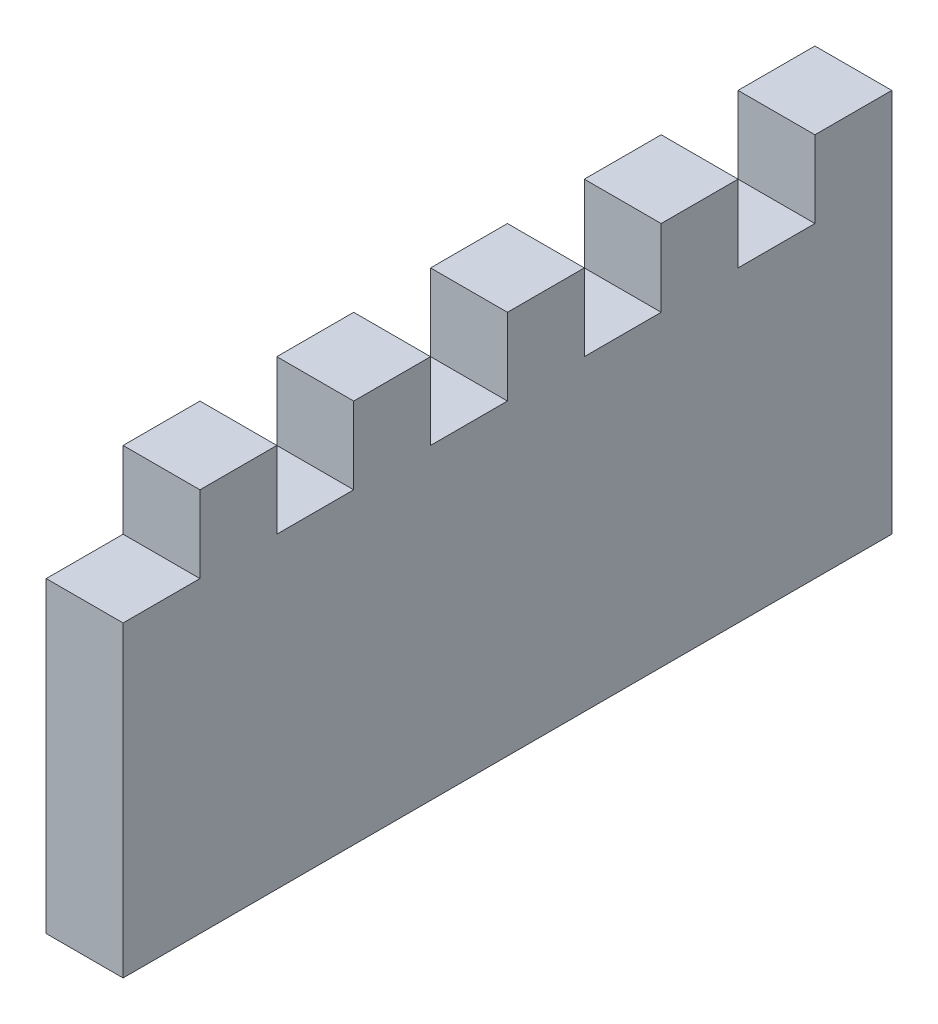
SolidWorks part; units mm, degrees
ref_plane "Plan de face" through (0, 0, 0) normal (0, 0, 1) x (1, 0, 0)
ref_plane "Plan de dessus" through (0, 0, 0) normal (0, 1, 0) x (1, 0, 0)
ref_plane "Plan de droite" through (0, 0, 0) normal (1, 0, 0) x (0, 0, -1)
sketch "Esquisse1" plane through (0, 0, 0) normal (1, 0, 0) x (0, 0, -1)
  line L1 (0, 0) -> (-100, 0)
  line L2 (0, 0) -> (0, 50)
  line L3 (0, 50) -> (-100, 50)
  line L4 (-100, 0) -> (-100, 50)
  dimension "D1" = 100
  dimension "D2" = 50
extrude "Boss.-Extru.1" add sketch "Esquisse1" along normal blind 10
sketch "Esquisse2" plane through (10, 0, 0) normal (1, 0, 0) x (0, 0, -1)
  line L0 (0, 50) -> (-100, 50) construction
  line L1 (-10, 50) -> (-20, 50)
  line L2 (-10, 50) -> (-10, 40)
  line L3 (-10, 40) -> (-20, 40)
  line L4 (-20, 50) -> (-20, 40)
  line L5 (0, 0) -> (0, 50) construction
  dimension "D1" = 10
  dimension "D2" = 10
  dimension "D3" = 10
extrude "Enlèv. mat.-Extru.1" cut sketch "Esquisse2" against normal blind 10
pattern_linear "Répétition linéaire1" count 5 spacing 20 along (0, 0, 1) of "Enlèv. mat.-Extru.1"
